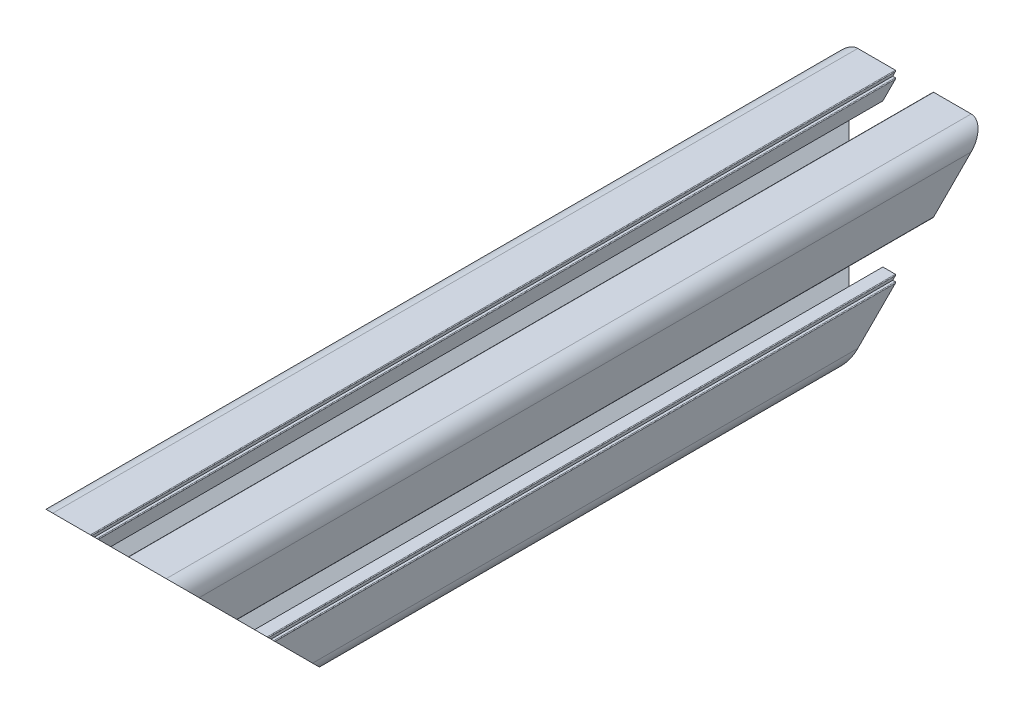
SolidWorks part; units mm, degrees
material "6061-T6 (SS)"
ref_plane "前视基准面" through (0, 0, 0) normal (0, 0, 1) x (1, 0, 0)
ref_plane "上视基准面" through (0, 0, 0) normal (0, 1, 0) x (1, 0, 0)
ref_plane "右视基准面" through (0, 0, 0) normal (1, 0, 0) x (0, 0, -1)
ref_plane "基准面1" through (0, 0, 50) normal (0, 0, 1) x (1, 0, 0)
sketch "草图1" plane through (0, 0, 50) normal (0, 0, 1) x (1, 0, 0)
  line L0 (-1518.245, 3588.0043) -> (-1518.245, 3582.9756)
  line L1 (-1518.245, 3582.9756) -> (-1522.9163, 3578.3043)
  line L2 (-1522.9163, 3578.3043) -> (-1533.6737, 3578.3043)
  line L3 (-1533.6737, 3578.3043) -> (-1538.345, 3582.9756)
  line L4 (-1538.345, 3582.9756) -> (-1538.345, 3588.0043)
  line L5 (-1538.345, 3588.0043) -> (-1534.845, 3588.0043)
  line L6 (-1534.845, 3588.0043) -> (-1534.845, 3586.3043)
  line L7 (-1534.845, 3586.3043) -> (-1532.445, 3586.3043)
  line L8 (-1532.445, 3586.3043) -> (-1532.445, 3589.7043)
  line L9 (-1532.645, 3589.9043) -> (-1533.345, 3589.9043)
  line L10 (-1533.345, 3589.9043) -> (-1533.345, 3590.6043)
  line L11 (-1533.545, 3590.8043) -> (-1543.795, 3590.8043)
  line L12 (-1548.295, 3586.3043) -> (-1548.295, 3576.0543)
  line L13 (-1548.095, 3575.8543) -> (-1547.395, 3575.8543)
  line L14 (-1547.395, 3575.8543) -> (-1547.395, 3575.1543)
  line L15 (-1547.195, 3574.9543) -> (-1543.795, 3574.9543)
  line L16 (-1543.795, 3574.9543) -> (-1543.795, 3577.3543)
  line L17 (-1543.795, 3577.3543) -> (-1545.495, 3577.3543)
  line L18 (-1545.495, 3577.3543) -> (-1545.495, 3580.8543)
  line L19 (-1545.495, 3580.8543) -> (-1540.4663, 3580.8543)
  line L20 (-1540.4663, 3580.8543) -> (-1535.795, 3576.183)
  line L21 (-1535.795, 3576.183) -> (-1535.795, 3565.4256)
  line L22 (-1535.795, 3565.4256) -> (-1540.4663, 3560.7543)
  line L23 (-1540.4663, 3560.7543) -> (-1545.495, 3560.7543)
  line L24 (-1545.495, 3560.7543) -> (-1545.495, 3564.2543)
  line L25 (-1545.495, 3564.2543) -> (-1543.795, 3564.2543)
  line L26 (-1543.795, 3564.2543) -> (-1543.795, 3566.6543)
  line L27 (-1543.795, 3566.6543) -> (-1547.195, 3566.6543)
  line L28 (-1547.395, 3566.4543) -> (-1547.395, 3565.7543)
  line L29 (-1547.395, 3565.7543) -> (-1548.095, 3565.7543)
  line L30 (-1548.295, 3565.5543) -> (-1548.295, 3555.3043)
  line L31 (-1543.795, 3550.8043) -> (-1533.545, 3550.8043)
  line L32 (-1533.345, 3551.0043) -> (-1533.345, 3551.7043)
  line L33 (-1533.345, 3551.7043) -> (-1532.645, 3551.7043)
  line L34 (-1532.445, 3551.9043) -> (-1532.445, 3555.3043)
  line L35 (-1532.445, 3555.3043) -> (-1534.845, 3555.3043)
  line L36 (-1534.845, 3555.3043) -> (-1534.845, 3553.6043)
  line L37 (-1534.845, 3553.6043) -> (-1538.345, 3553.6043)
  line L38 (-1538.345, 3553.6043) -> (-1538.345, 3558.633)
  line L39 (-1538.345, 3558.633) -> (-1533.6737, 3563.3043)
  line L40 (-1533.6737, 3563.3043) -> (-1522.9163, 3563.3043)
  line L41 (-1522.9163, 3563.3043) -> (-1518.245, 3558.633)
  line L42 (-1518.245, 3558.633) -> (-1518.245, 3553.6043)
  line L43 (-1518.245, 3553.6043) -> (-1521.745, 3553.6043)
  line L44 (-1521.745, 3553.6043) -> (-1521.745, 3555.3043)
  line L45 (-1521.745, 3555.3043) -> (-1524.145, 3555.3043)
  line L46 (-1524.145, 3555.3043) -> (-1524.145, 3551.9043)
  line L47 (-1523.945, 3551.7043) -> (-1523.245, 3551.7043)
  line L48 (-1523.245, 3551.7043) -> (-1523.245, 3551.0043)
  line L49 (-1523.045, 3550.8043) -> (-1512.795, 3550.8043)
  line L50 (-1508.295, 3555.3043) -> (-1508.295, 3565.5543)
  line L51 (-1508.495, 3565.7543) -> (-1509.195, 3565.7543)
  line L52 (-1509.195, 3565.7543) -> (-1509.195, 3566.4543)
  line L53 (-1509.395, 3566.6543) -> (-1512.795, 3566.6543)
  line L54 (-1512.795, 3566.6543) -> (-1512.795, 3564.2543)
  line L55 (-1512.795, 3564.2543) -> (-1511.095, 3564.2543)
  line L56 (-1511.095, 3564.2543) -> (-1511.095, 3560.7543)
  line L57 (-1511.095, 3560.7543) -> (-1516.1237, 3560.7543)
  line L58 (-1516.1237, 3560.7543) -> (-1520.795, 3565.4256)
  line L59 (-1520.795, 3565.4256) -> (-1520.795, 3576.183)
  line L60 (-1520.795, 3576.183) -> (-1516.1237, 3580.8543)
  line L61 (-1516.1237, 3580.8543) -> (-1511.095, 3580.8543)
  line L62 (-1511.095, 3580.8543) -> (-1511.095, 3577.3543)
  line L63 (-1511.095, 3577.3543) -> (-1512.795, 3577.3543)
  line L64 (-1512.795, 3577.3543) -> (-1512.795, 3574.9543)
  line L65 (-1512.795, 3574.9543) -> (-1509.395, 3574.9543)
  line L66 (-1509.195, 3575.1543) -> (-1509.195, 3575.8543)
  line L67 (-1509.195, 3575.8543) -> (-1508.495, 3575.8543)
  line L68 (-1508.295, 3576.0543) -> (-1508.295, 3586.3043)
  line L69 (-1512.795, 3590.8043) -> (-1523.045, 3590.8043)
  line L70 (-1523.245, 3590.6043) -> (-1523.245, 3589.9043)
  line L71 (-1523.245, 3589.9043) -> (-1523.945, 3589.9043)
  line L72 (-1524.145, 3589.7043) -> (-1524.145, 3586.3043)
  line L73 (-1524.145, 3586.3043) -> (-1521.745, 3586.3043)
  line L74 (-1521.745, 3586.3043) -> (-1521.745, 3588.0043)
  line L75 (-1521.745, 3588.0043) -> (-1518.245, 3588.0043)
  circle A0 centre (-1513.27, 3555.7793) radius 2.95
  circle A1 centre (-1528.295, 3570.8043) radius 3.4
  circle A2 centre (-1513.27, 3585.8293) radius 2.95
  arc A3 (-1532.445, 3589.7043) -> (-1532.645, 3589.9043) centre (-1532.645, 3589.7043) ccw
  arc A4 (-1533.345, 3590.6043) -> (-1533.545, 3590.8043) centre (-1533.545, 3590.6043) ccw
  arc A5 (-1543.795, 3590.8043) -> (-1548.295, 3586.3043) centre (-1543.795, 3586.3043) ccw
  arc A6 (-1548.295, 3576.0543) -> (-1548.095, 3575.8543) centre (-1548.095, 3576.0543) ccw
  arc A7 (-1547.395, 3575.1543) -> (-1547.195, 3574.9543) centre (-1547.195, 3575.1543) ccw
  arc A8 (-1547.195, 3566.6543) -> (-1547.395, 3566.4543) centre (-1547.195, 3566.4543) ccw
  arc A9 (-1548.095, 3565.7543) -> (-1548.295, 3565.5543) centre (-1548.095, 3565.5543) ccw
  arc A10 (-1548.295, 3555.3043) -> (-1543.795, 3550.8043) centre (-1543.795, 3555.3043) ccw
  arc A11 (-1533.545, 3550.8043) -> (-1533.345, 3551.0043) centre (-1533.545, 3551.0043) ccw
  arc A12 (-1532.645, 3551.7043) -> (-1532.445, 3551.9043) centre (-1532.645, 3551.9043) ccw
  arc A13 (-1524.145, 3551.9043) -> (-1523.945, 3551.7043) centre (-1523.945, 3551.9043) ccw
  arc A14 (-1523.245, 3551.0043) -> (-1523.045, 3550.8043) centre (-1523.045, 3551.0043) ccw
  arc A15 (-1512.795, 3550.8043) -> (-1508.295, 3555.3043) centre (-1512.795, 3555.3043) ccw
  arc A16 (-1508.295, 3565.5543) -> (-1508.495, 3565.7543) centre (-1508.495, 3565.5543) ccw
  arc A17 (-1509.195, 3566.4543) -> (-1509.395, 3566.6543) centre (-1509.395, 3566.4543) ccw
  arc A18 (-1509.395, 3574.9543) -> (-1509.195, 3575.1543) centre (-1509.395, 3575.1543) ccw
  arc A19 (-1508.495, 3575.8543) -> (-1508.295, 3576.0543) centre (-1508.495, 3576.0543) ccw
  arc A20 (-1508.295, 3586.3043) -> (-1512.795, 3590.8043) centre (-1512.795, 3586.3043) ccw
  arc A21 (-1523.045, 3590.8043) -> (-1523.245, 3590.6043) centre (-1523.045, 3590.6043) ccw
  arc A22 (-1523.945, 3589.9043) -> (-1524.145, 3589.7043) centre (-1523.945, 3589.7043) ccw
  circle A23 centre (-1543.32, 3585.8293) radius 2.95
  circle A24 centre (-1543.32, 3555.7793) radius 2.95
extrude "凸台-拉伸1" add sketch "草图1" against normal mid plane 220
ref_plane "基准面2" through (-1528.295, 0, 0) normal (1, 0, 0) x (0, 0, -1)
ref_plane "基准面3" through (0, 3570.8043, 0) normal (0, 1, 0) x (1, 0, 0)
sketch "草图2" plane through (-1508.295, 0, 0) normal (1, 0, 0) x (0, 0, -1)
  line L0 (60, 3590.8043) -> (60, 3550.8043)
  line L1 (60, 3550.8043) -> (20, 3550.8043)
  line L2 (60, 3550.8043) -> (-160, 3550.8043) construction
  line L3 (20, 3550.8043) -> (60, 3590.8043)
  line L4 (-160, 3590.8043) -> (-160, 3550.8043)
  line L5 (-160, 3550.8043) -> (-120, 3550.8043)
  line L6 (-120, 3550.8043) -> (-160, 3590.8043)
  dimension "D1" = 45
  dimension "D2" = 45
extrude "切除-拉伸1" cut sketch "草图2" against normal blind 86
